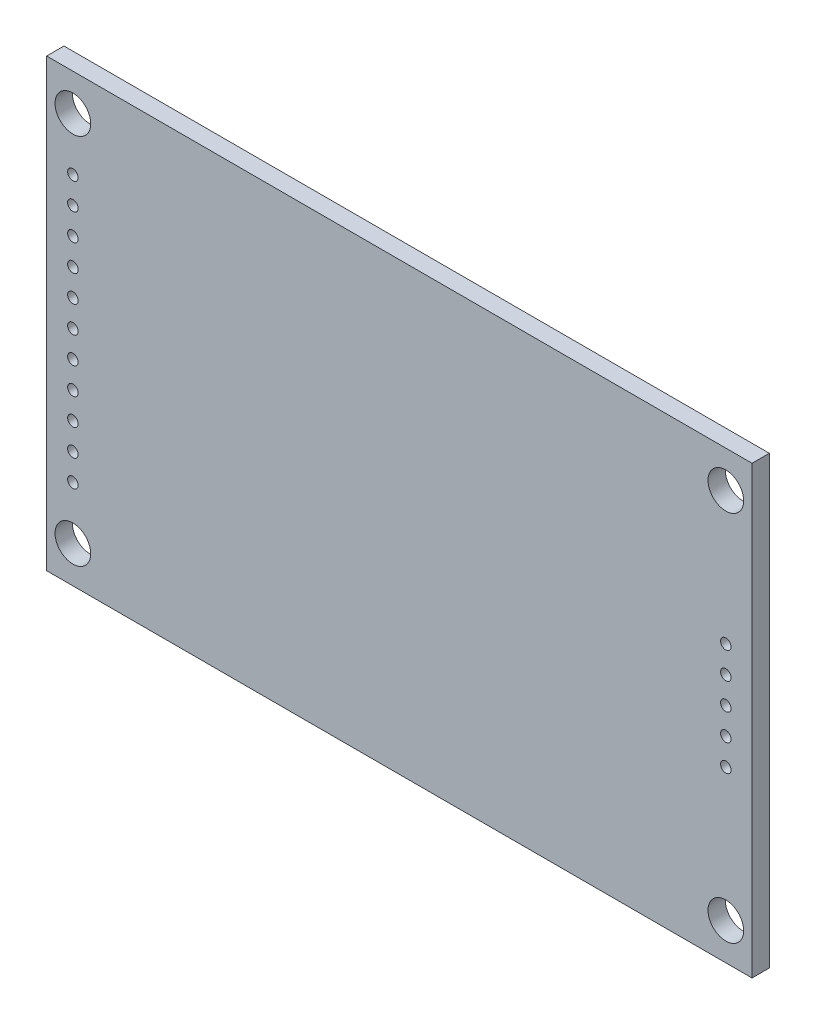
SolidWorks part; units mm, degrees
ref_plane "Front Plane" through (0, 0, 0) normal (0, 0, 1) x (1, 0, 0)
ref_plane "Top Plane" through (0, 0, 0) normal (0, 1, 0) x (1, 0, 0)
ref_plane "Right Plane" through (0, 0, 0) normal (1, 0, 0) x (0, 0, -1)
sketch "Sketch2" plane through (0, 0, 0) normal (0, 0, 1) x (1, 0, 0)
  line L1 (-33.625, -21.25) -> (33.625, -21.25)
  line L2 (-33.625, -21.25) -> (-33.625, 21.25)
  line L3 (-33.625, 21.25) -> (33.625, 21.25)
  line L4 (33.625, -21.25) -> (33.625, 21.25)
  line L5 (-33.625, -21.25) -> (33.625, 21.25) construction
  line L6 (-33.625, 21.25) -> (33.625, -21.25) construction
  point P0 (0, 0)
  point P6 (-33.625, 0)
  dimension "D1" = 42.5
  dimension "D2" = 67.25
extrude "Boss-Extrude1" add sketch "Sketch2" along normal blind 1.65
sketch "Sketch3" plane through (0, 0, 0) normal (0, 0, -1) x (-1, 0, 0)
  line L0 (33.625, -21.25) -> (-33.625, -21.25) construction
  line L1 (33.625, 21.25) -> (33.625, -21.25) construction
  line L2 (-33.625, 21.25) -> (33.625, 21.25) construction
  line L3 (-33.625, -21.25) -> (-33.625, 21.25) construction
  circle A0 centre (31.125, -17.75) radius 1.7
  circle A1 centre (31.125, 17.75) radius 1.7
  circle A2 centre (-31.125, -17.75) radius 1.7
  circle A3 centre (-31.125, 17.75) radius 1.7
  dimension "D1" = 3.4
  dimension "D2" = 3.5
  dimension "D4" = 3.4
  dimension "D7" = 3.4
  dimension "D10" = 3.4
  dimension "D12" = 3.5
  dimension "D3" = 2.5
  dimension "D5" = 3.5
  dimension "D6" = 2.5
  dimension "D8" = 3.5
  dimension "D9" = 2.5
  dimension "D11" = 2.5
extrude "Cut-Extrude1" cut sketch "Sketch3" against normal blind 1.65
sketch "Sketch4" plane through (0, 0, 1.65) normal (0, 0, 1) x (1, 0, 0)
  line L0 (-355.1219, 60.0833) -> (-355.1219, 385.4167) construction
sketch "Sketch5" plane through (0, 0, 1.65) normal (0, 0, 1) x (1, 0, 0)
  line L0 (-31.125, 17.75) -> (-31.125, -17.75) construction
  circle A0 centre (-31.125, 0) radius 0.5
  circle A1 centre (-31.125, -2.54) radius 0.5
  circle A2 centre (-31.125, -5.08) radius 0.5
  circle A3 centre (-31.125, -7.62) radius 0.5
  circle A4 centre (-31.125, -10.16) radius 0.5
  circle A5 centre (-31.125, -12.7) radius 0.5
  circle A6 centre (-31.125, 2.54) radius 0.5
  circle A7 centre (-31.125, 5.08) radius 0.5
  circle A8 centre (-31.125, 7.62) radius 0.5
  circle A9 centre (-31.125, 10.16) radius 0.5
  circle A10 centre (-31.125, 12.7) radius 0.5
  dimension "D1" = 1
  dimension "D2" = 6
  dimension "D3" = 6
extrude "Cut-Extrude2" cut sketch "Sketch5" against normal blind 1.65
sketch "Sketch6" plane through (0, 0, 1.65) normal (0, 0, 1) x (1, 0, 0)
  line L0 (-31.625, 12.7) -> (-30.625, 12.7) construction
  circle A0 centre (-31.125, 12.7) radius 0.5 construction
  point P5 (-31.125, 12.7)
ref_plane "Plane1" through (-31.125, 0, 0) normal (-1, 0, 0) x (0, 0, 1)
sketch "Sketch7" plane through (-31.125, 0, 0) normal (-1, 0, 0) x (0, 0, 1)
  line L0 (1.65, 12.7) -> (6.9139, 12.7) construction
sketch "Sketch8" plane through (0, 0, 1.65) normal (0, 0, 1) x (1, 0, 0)
  line L0 (31.125, 17.75) -> (31.125, -17.75) construction
  line L1 (31.125, 20.29) -> (31.125, -15.21) construction
  line L2 (31.125, 22.83) -> (31.125, -12.67) construction
  line L3 (31.125, 15.21) -> (31.125, -20.29) construction
  line L4 (31.125, 12.67) -> (31.125, -22.83) construction
  circle A0 centre (31.125, 0) radius 0.5
  circle A1 centre (31.125, 2.54) radius 0.5
  circle A2 centre (31.125, 5.08) radius 0.5
  circle A3 centre (31.125, -2.54) radius 0.5
  circle A4 centre (31.125, -5.08) radius 0.5
  dimension "D1" = 1
  dimension "D2" = 3
  dimension "D3" = 3
extrude "Cut-Extrude3" cut sketch "Sketch8" against normal blind 1.65
